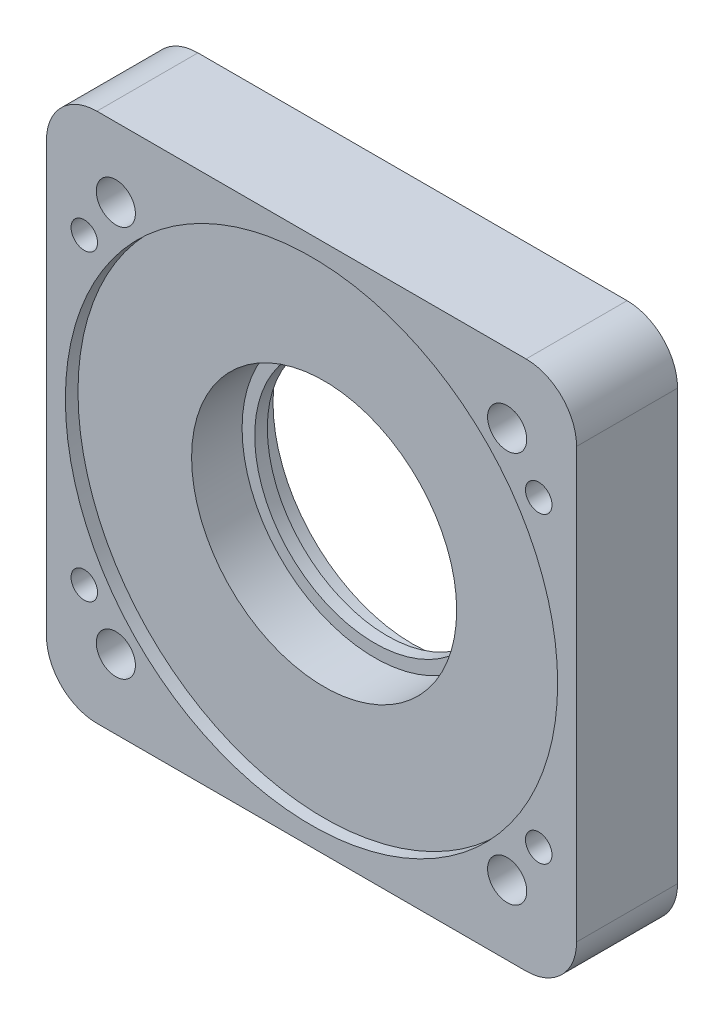
SolidWorks part; units mm, degrees
ref_plane "前视基准面" through (0, 0, 0) normal (0, 0, 1) x (1, 0, 0)
ref_plane "上视基准面" through (0, 0, 0) normal (0, 1, 0) x (1, 0, 0)
ref_plane "右视基准面" through (0, 0, 0) normal (1, 0, 0) x (0, 0, -1)
sketch "草图1" plane through (0, 0, 0) normal (0, 0, 1) x (1, 0, 0)
  line L1 (-21, 21) -> (21, 21)
  line L2 (-21, 21) -> (-21, -21)
  line L3 (-21, -21) -> (21, -21)
  line L4 (21, 21) -> (21, -21)
  line L5 (0, -21) -> (0, 21) construction
  line L6 (-21, 0) -> (21, 0) construction
  point P0 (0, 0)
  dimension "D1" = 42
  dimension "D2" = 42
extrude "凸台-拉伸1" add sketch "草图1" along normal blind 8
sketch "草图2" plane through (0, 0, 8) normal (0, 0, 1) x (1, 0, 0)
  circle A0 centre (0, 0) radius 9.5
  dimension "D1" = 19
extrude "切除-拉伸1" cut sketch "草图2" against normal through all
sketch "草图3" plane through (0, 0, 8) normal (0, 0, 1) x (1, 0, 0)
  circle A0 centre (0, 0) radius 10.5
  dimension "D1" = 21
extrude "切除-拉伸2" cut sketch "草图3" against normal offset from surface (5 mm away) 3 up to face at (9.5, 0, 0)
sketch "草图6" plane through (0, 0, 0) normal (0, 0, -1) x (-1, 0, 0)
  circle A0 centre (0, 0) radius 11.05
  dimension "D1" = 22.1
extrude "切除-拉伸3" cut sketch "草图6" against normal blind 2
fillet "圆角1" radius 4 4 edges at (21, -21, 4) (21, 21, 4) (-21, 21, 4) (-21, -21, 4)
sketch "草图7" plane through (0, 0, 8) normal (0, 0, 1) x (1, 0, 0)
  line L0 (-21, 17) -> (-21, -17) construction
  line L2 (-21, -9) -> (-21, -13)
  line L3 (-21, -13) -> (-17, -13)
  line L5 (-21, -9) -> (-17, -13)
  line L6 (-17, -21) -> (17, -21) construction
  line L7 (-9, 21) -> (-13, 17)
  line L8 (-13, 21) -> (-13, 17)
  line L9 (-9, 21) -> (-13, 21)
  line L10 (21, 9) -> (17, 13)
  line L11 (21, 13) -> (17, 13)
  line L12 (21, 9) -> (21, 13)
  line L13 (9, -21) -> (13, -17)
  line L14 (13, -21) -> (13, -17)
  line L15 (9, -21) -> (13, -21)
  point P19 (0, 0)
  dimension "D1" = 4
  dimension "D2" = 4
  dimension "D3" = 8
  dimension "D4" = 4
extrude "凸台-拉伸2" [suppressed] add sketch "草图7" along normal blind 4
sketch "草图8" plane through (0, 0, 8) normal (0, 0, 1) x (1, 0, 0)
  circle A0 centre (0, 0) radius 19.5
  dimension "D1" = 39
extrude "切除-拉伸4" cut sketch "草图8" against normal blind 1
sketch "草图9" plane through (0, 0, 0) normal (0, 0, -1) x (-1, 0, 0)
  circle A0 centre (-15.5, 15.5) radius 1.55
  circle A1 centre (15.5, 15.5) radius 1.55
  circle A2 centre (15.5, -15.5) radius 1.55
  circle A3 centre (-15.5, -15.5) radius 1.55
  point P12 (0, 0)
  dimension "D3" = 3.1
  dimension "D1" = 15.5
  dimension "D2" = 15.5
  dimension "D4" = 4
extrude "切除-拉伸5" cut sketch "草图9" against normal through all
sketch "草图10" plane through (0, 0, 0) normal (0, 0, -1) x (-1, 0, 0)
  line L0 (-17, 21) -> (17, 21) construction
  line L1 (-21, -17) -> (-21, 17) construction
  line L2 (-24.4871, 0) -> (30.2423, 0) construction
  line L3 (0, 24.9065) -> (0, -25.9269) construction
  circle A0 centre (-18, 12) radius 1.55
  circle A1 centre (18, 12) radius 1.55
  circle A2 centre (18, -12) radius 1.55
  circle A3 centre (-18, -12) radius 1.55
  dimension "D1" = 3.1
  dimension "D2" = 9
  dimension "D3" = 3
extrude "切除-拉伸6" cut sketch "草图10" against normal through all
sketch "草图11" plane through (0, 0, 8) normal (0, 0, 1) x (1, 0, 0)
  line L0 (24.4871, 0) -> (-30.2423, 0) construction
  line L1 (0, 24.9065) -> (0, -25.9269) construction
  line L2 (24.4871, 0) -> (-30.2423, 0) construction
  line L3 (0, 24.9065) -> (0, -25.9269) construction
  circle A0 centre (-18, 12) radius 1.55
  circle A1 centre (-18, 12) radius 1.05
  circle A2 centre (18, 12) radius 1.05
  circle A3 centre (18, 12) radius 1.55
  circle A4 centre (18, -12) radius 1.55
  circle A5 centre (18, -12) radius 1.05
  circle A6 centre (-18, -12) radius 1.55
  circle A7 centre (-18, -12) radius 1.05
  dimension "D1" = 3.1
  dimension "D2" = 2.1
extrude "凸台-拉伸3" add sketch "草图11" against normal blind 2
